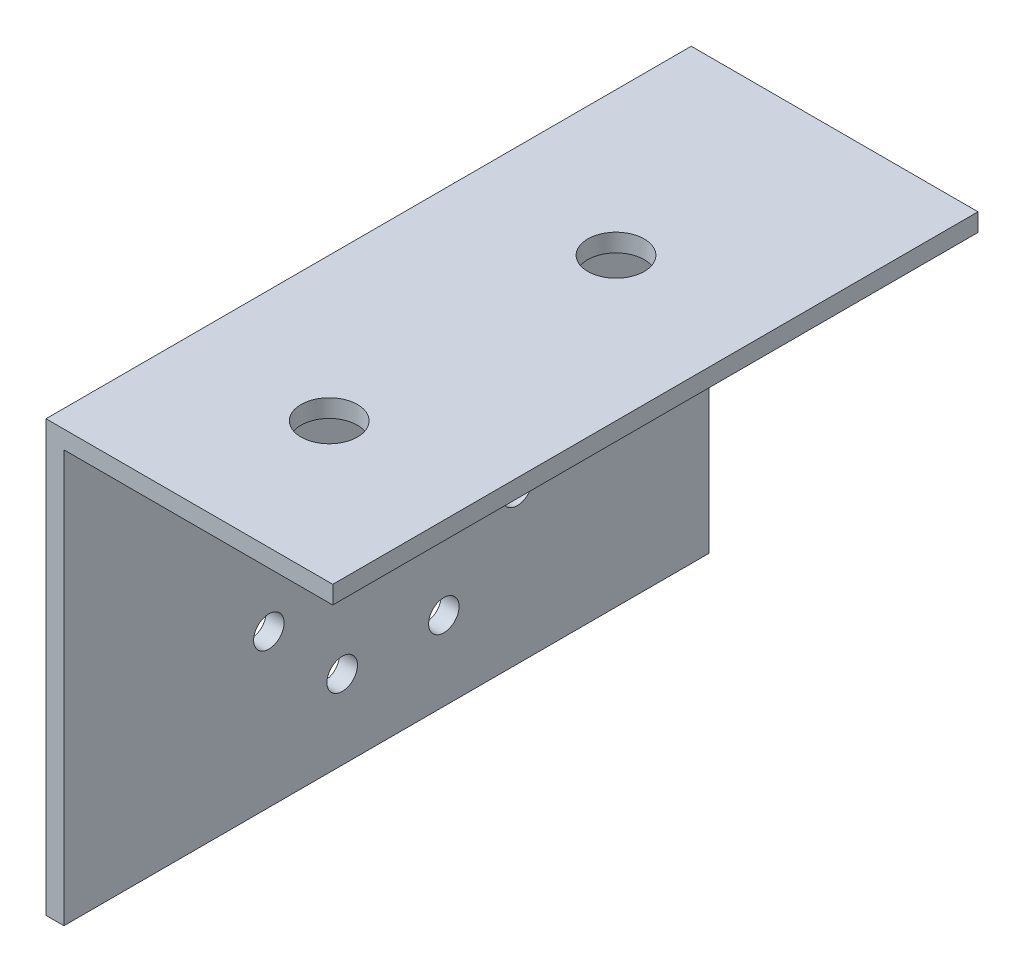
SolidWorks part; units mm, degrees
ref_plane "Front Plane" through (0, 0, 0) normal (0, 0, 1) x (1, 0, 0)
ref_plane "Top Plane" through (0, 0, 0) normal (0, 1, 0) x (1, 0, 0)
ref_plane "Right Plane" through (0, 0, 0) normal (1, 0, 0) x (0, 0, -1)
sketch "Sketch1" plane through (0, 0, 0) normal (0, 0, 1) x (1, 0, 0)
  line L0 (-0.2517, 27.3813) -> (-25.6517, 27.3813)
  line L1 (-25.6517, -10.7187) -> (-24.0642, -10.7187)
  line L2 (-25.6517, -10.7187) -> (-25.6517, 27.3813)
  line L4 (-24.0642, -10.7187) -> (-24.0642, 25.7938)
  line L7 (-24.0642, 25.7938) -> (-0.2517, 25.7938)
  line L8 (-0.2517, 27.3813) -> (-0.2517, 25.7938)
  dimension "D1" = 38.1
  dimension "D2" = 25.4
  dimension "D3" = 1.5875
  dimension "D4" = 1.5875
extrude "Boss-Extrude1" add sketch "Sketch1" along normal blind 57.15
sketch "Sketch2" plane through (0, 25.7938, 0) normal (0, -1, 0) x (1, 0, 0)
  line L3 (-0.2517, 57.15) -> (-0.2517, 0) construction
  circle A0 centre (-12.9517, 44.763) radius 2.5
  circle A1 centre (-12.9517, 19.363) radius 2.5
  dimension "D1" = 5
  dimension "D2" = 5
  dimension "D3" = 25.4
  dimension "D4" = 12.7
sketch "Sketch3" plane through (-24.0642, 0, 0) normal (1, 0, 0) x (0, 0, -1)
  line L0 (-57.15, -10.7187) -> (0, -10.7187) construction
  line L1 (0, -10.7187) -> (0, 25.7938) construction
  line L4 (-28, 7.2813) -> (-28, 23.7514) construction
  circle A0 centre (-28, 18.2813) radius 1.35
  circle A1 centre (-20.2218, 15.0594) radius 1.35
  circle A2 centre (-17, 7.2813) radius 1.35
  circle A3 centre (-20.2218, -0.4969) radius 1.35
  circle A4 centre (-28, -3.7187) radius 1.35
  circle A5 centre (-35.7782, -0.4969) radius 1.35
  circle A6 centre (-39, 7.2813) radius 1.35
  circle A7 centre (-35.7782, 15.0594) radius 1.35
  circle A8 centre (-32.5, 18.2813) radius 1.35
  circle A9 centre (-23.5, 18.2813) radius 1.35
  circle A10 centre (-17, 11.7813) radius 1.35
  circle A11 centre (-17, 2.7813) radius 1.35
  circle A12 centre (-23.5, -3.7187) radius 1.35
  circle A13 centre (-32.5, -3.7187) radius 1.35
  circle A14 centre (-39, 2.7813) radius 1.35
  circle A15 centre (-39, 11.7813) radius 1.35
  point P0 (-28, 7.2813)
  dimension "D3" = 8
  dimension "D4" = 2.7
  dimension "D5" = 2.7
  dimension "D7" = 2.7
  dimension "D10" = 11
  dimension "D12" = 2.7
  dimension "D13" = 2.7
  dimension "D1" = 18
  dimension "D2" = 28
  dimension "D6" = 11
  dimension "D8" = 4.5
  dimension "D9" = 4.5
  dimension "D11" = 11
  dimension "D14" = 4.5
  dimension "D15" = 4.5
  dimension "D16" = 4.5
  dimension "D17" = 4.5
  dimension "D18" = 4.5
  dimension "D19" = 4.5
extrude "Cut-Extrude1" cut sketch "Sketch3" against normal through all contours A14 | A15 | A8 | A9 | A10 | A11 | A12 | A13
extrude "Cut-Extrude2" cut sketch "Sketch2" against normal through all
